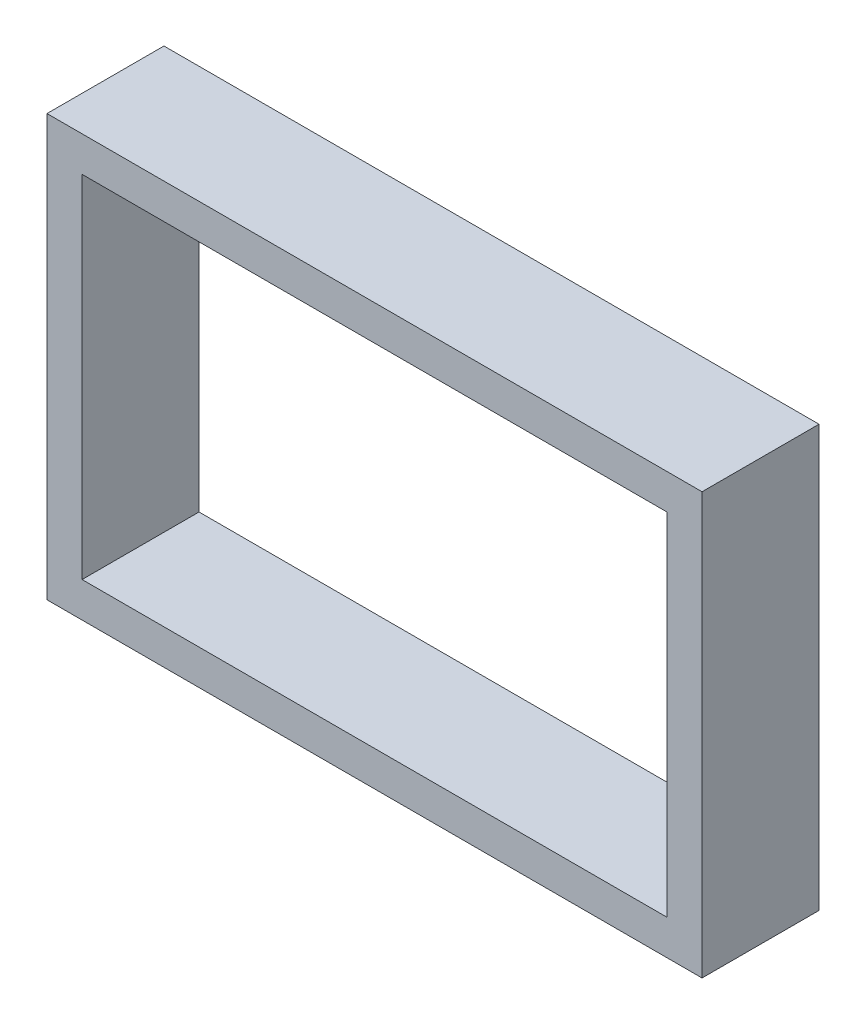
SolidWorks part; units mm, degrees
ref_plane "前基準面" through (0, 0, 0) normal (0, 0, 1) x (1, 0, 0)
ref_plane "上基準面" through (0, 0, 0) normal (0, 1, 0) x (1, 0, 0)
ref_plane "右基準面" through (0, 0, 0) normal (1, 0, 0) x (0, 0, -1)
sketch "草圖1" plane through (0, 0, 0) normal (0, 0, 1) x (1, 0, 0)
  line L0 (0, -55) -> (0, 55) construction
  line L1 (-25, 15) -> (25, 15)
  line L2 (-25, 15) -> (-25, -15)
  line L3 (-25, -15) -> (25, -15)
  line L4 (25, 15) -> (25, -15)
  line L5 (55, 0) -> (-55, 0) construction
  line L6 (-28, 18) -> (28, 18)
  line L7 (28, 18) -> (28, -18)
  line L8 (-28, -18) -> (28, -18)
  line L9 (-28, 18) -> (-28, -18)
  dimension "D1" = 50
  dimension "D2" = 30
  dimension "D3" = 25
  dimension "D4" = 15
  dimension "D5" = 3
extrude "填料-伸長1" add sketch "草圖1" along normal blind 10
